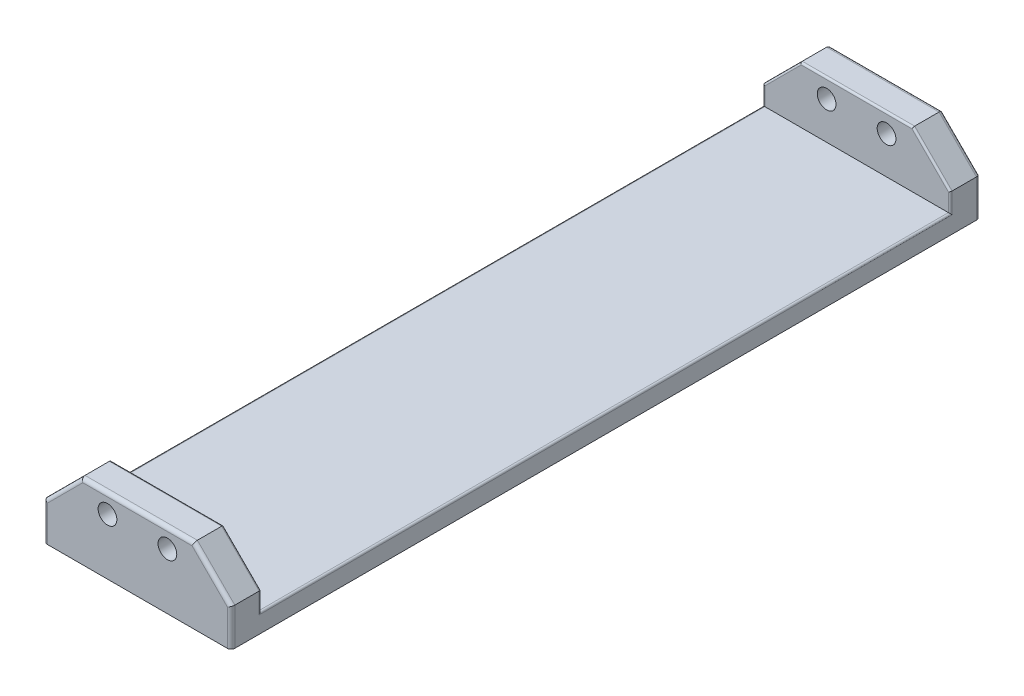
SolidWorks part; units mm, degrees
ref_plane "Front Plane" through (0, 0, 0) normal (0, 0, 1) x (1, 0, 0)
ref_plane "Top Plane" through (0, 0, 0) normal (0, 1, 0) x (1, 0, 0)
ref_plane "Right Plane" through (0, 0, 0) normal (1, 0, 0) x (0, 0, -1)
sketch "Sketch1" plane through (0, 0, 0) normal (0, 0, 1) x (1, 0, 0)
  line L1 (-250, 100) -> (250, 100)
  line L2 (-250, 100) -> (-250, -100)
  line L3 (-250, -100) -> (250, -100)
  line L4 (250, 100) -> (250, -100)
  line L5 (-250, 100) -> (250, -100) construction
  line L6 (-250, -100) -> (250, 100) construction
  point P0 (0, 0)
  dimension "D1" = 500
  dimension "D2" = 200
extrude "Boss-Extrude1" add sketch "Sketch1" along normal blind 2000
sketch "Sketch2" plane through (0, 0, 2000) normal (0, 0, 1) x (1, 0, 0)
  line L0 (-250, 0) -> (-150, 100)
  line L1 (-250, 100) -> (-250, -100) construction
  line L2 (250, 100) -> (-250, 100) construction
  line L3 (250, 0) -> (150, 100)
  line L4 (250, -100) -> (250, 100) construction
  line L5 (150, 100) -> (250, 100)
  line L6 (250, 100) -> (250, 0)
  line L7 (-250, 0) -> (-250, 100)
  line L8 (-250, 100) -> (-150, 100)
  dimension "D1" = 45
  dimension "D2" = 45
sketch "Sketch3" plane through (-250, 0, 0) normal (-1, 0, 0) x (0, 0, 1)
  line L0 (2000, 100) -> (0, 100) construction
  line L1 (80, 100) -> (1920, 100)
  line L2 (80, 100) -> (80, -50)
  line L3 (80, -50) -> (1920, -50)
  line L4 (1920, 100) -> (1920, -50)
  line L5 (0, 100) -> (0, -100) construction
  line L6 (2000, 100) -> (2000, -100) construction
  dimension "D1" = 80
  dimension "D2" = 80
  dimension "D3" = 150
extrude "Cut-Extrude1" cut sketch "Sketch3" against normal blind 1000
extrude "Cut-Extrude2" cut sketch "Sketch2" against normal through all
sketch "Sketch4" plane through (0, 0, 2000) normal (0, 0, 1) x (1, 0, 0)
  line L0 (-200, 50) -> (200, 50) construction
  line L1 (-250, 0) -> (-150, 100) construction
  line L2 (150, 100) -> (250, 0) construction
  line L3 (150, 100) -> (-150, 100) construction
  circle A0 centre (-80, 50) radius 25
  circle A1 centre (80, 50) radius 25
  point P10 (0, 100)
  point P13 (0, 100)
  dimension "D3" = 50
  dimension "D1" = 80
  dimension "D2" = 80
extrude "Cut-Extrude3" cut sketch "Sketch4" against normal through all
fillet "Fillet1" radius 10 5 edges at (250, -50, 2000) (200, 50, 2000) (0, 100, 2000) (-200, 50, 2000) (-250, -50, 2000)
fillet "Fillet2" radius 10 5 edges at (-250, -50, 0) (-200, 50, 0) (0, 100, 0) (200, 50, 0) (250, -50, 0)
fillet "Fillet4" radius 5 12 edges at (200, 50, 1920) (-250, -25, 1920) (-200, 50, 1920) (0, 100, 1920) (250, -25, 1920) (250, -25, 80) (200, 50, 80) (-250, -25, 80) (-200, 50, 80) (0, 100, 80) (250, -50, 1000) (-250, -50, 1000)
